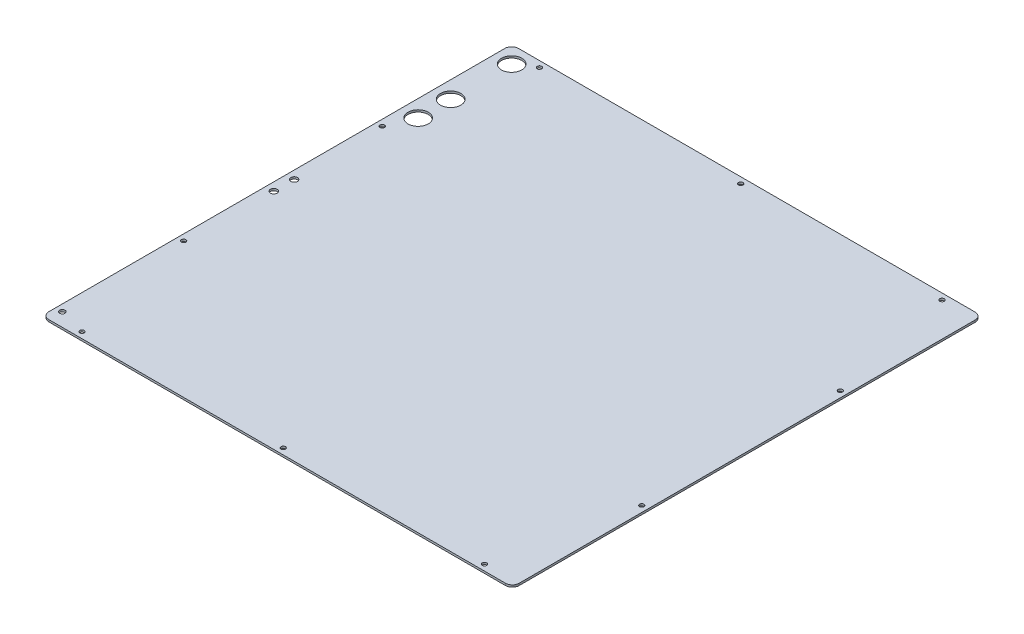
SolidWorks part; units mm, degrees
ref_plane "Front Plane" through (0, 0, 0) normal (0, 0, 1) x (1, 0, 0)
ref_plane "Top Plane" through (0, 0, 0) normal (0, 1, 0) x (1, 0, 0)
ref_plane "Right Plane" through (0, 0, 0) normal (1, 0, 0) x (0, 0, -1)
sketch "Sketch1" plane through (0, 0, 0) normal (0, 1, 0) x (1, 0, 0)
  line L0 (0, 0) -> (0, 346.5) construction
  line L1 (347, -346.5) -> (-347, -346.5)
  line L2 (347, -346.5) -> (347, 346.5)
  line L3 (347, 346.5) -> (-347, 346.5)
  line L4 (-347, -346.5) -> (-347, 346.5)
  line L5 (347, 0) -> (0, 0) construction
  point P0 (0, 0)
  dimension "D1" = 693
  dimension "D3" = 694
extrude "Boss-Extrude1" add sketch "Sketch1" along normal blind 3
hole_wizard "M6 Clearance Hole1" positions "Sketch2" profile "Sketch3" hole size "M6" standard "ISO" end condition through all
sketch "Sketch2" plane through (0, 3, 0) normal (0, 1, 0) x (1, 0, 0)
  line L0 (-347, -346.5) -> (347, -346.5) construction
  line L1 (347, -346.5) -> (347, 346.5) construction
  point P0 (297, -337.5)
  dimension "D1" = 9
  dimension "D2" = 50
sketch "Sketch3" plane through (297, 3, 337.5) normal (1, 0, 0) x (0, 0, 1)
  line L0 (0, 0) -> (0, 3)
  line L1 (0, 3) -> (3.3, 3)
  line L2 (3.3, 3) -> (3.3, 0)
  line L5 (3.3, 0) -> (0, 0)
  line L11 (0, -6.35) -> (0, 107.95) construction
  dimension "Thru Hole Dia." = 6.6
  dimension "Thru Hole Depth" = 3
pattern_linear "LPattern1" count 3 spacing 297 along (-1, 0, 0) of "M6 Clearance Hole1"
mirror "Mirror1" about plane through (0, 0, 0) normal (0, 0, 1) of "LPattern1", "M6 Clearance Hole1"
hole_wizard "M6 Clearance Hole2" positions "Sketch4" profile "Sketch5" hole size "M6" standard "ISO" end condition through all
sketch "Sketch4" plane through (0, 3, 0) normal (0, 1, 0) x (1, 0, 0)
  line L0 (347, -346.5) -> (347, 346.5) construction
  line L1 (-347, -346.5) -> (347, -346.5) construction
  point P0 (338, -146.5)
  dimension "D1" = 9
  dimension "D2" = 200
sketch "Sketch5" plane through (338, 3, 146.5) normal (1, 0, 0) x (0, 0, 1)
  line L0 (0, 0) -> (0, 3)
  line L1 (0, 3) -> (3.3, 3)
  line L2 (3.3, 3) -> (3.3, 0)
  line L5 (3.3, 0) -> (0, 0)
  line L11 (0, -6.35) -> (0, 107.95) construction
  dimension "Thru Hole Dia." = 6.6
  dimension "Thru Hole Depth" = 3
pattern_linear "LPattern2" count 2 spacing 293 along (0, 0, -1) of "M6 Clearance Hole2"
mirror "Mirror2" about plane through (0, 0, 0) normal (1, 0, 0) of "LPattern2", "M6 Clearance Hole2"
fillet "Fillet1" radius 10 4 edges at (-347, 1.5, -346.5) (347, 1.5, -346.5) (-347, 1.5, 346.5) (347, 1.5, 346.5)
sketch "Sketch6" plane through (0, 3, 0) normal (0, 1, 0) x (1, 0, 0)
  line L0 (-347, 336.5) -> (-347, -336.5) construction
  line L1 (-337, -346.5) -> (337, -346.5) construction
  line L2 (-335, -16.5) -> (-335, 13.5) construction
  line L3 (-322, 183.5) -> (-322, 231.5) construction
  line L4 (-322, 231.5) -> (-322, 321.5) construction
  line L5 (337, 346.5) -> (-337, 346.5) construction
  circle A0 centre (-337, -326.5) radius 4
  circle A1 centre (-335, -16.5) radius 5
  circle A2 centre (-335, 13.5) radius 5
  circle A3 centre (-322, 183.5) radius 15
  circle A4 centre (-322, 231.5) radius 15
  circle A5 centre (-322, 321.5) radius 15
  dimension "D3" = 8
  dimension "D4" = 10
  dimension "D8" = 30
  dimension "D11" = 90
  dimension "D1" = 10
  dimension "D2" = 20
  dimension "D5" = 30
  dimension "D6" = 330
  dimension "D7" = 12
  dimension "D9" = 25
  dimension "D10" = 530
  dimension "D12" = 25
extrude "Cut-Extrude1" cut sketch "Sketch6" against normal through all
